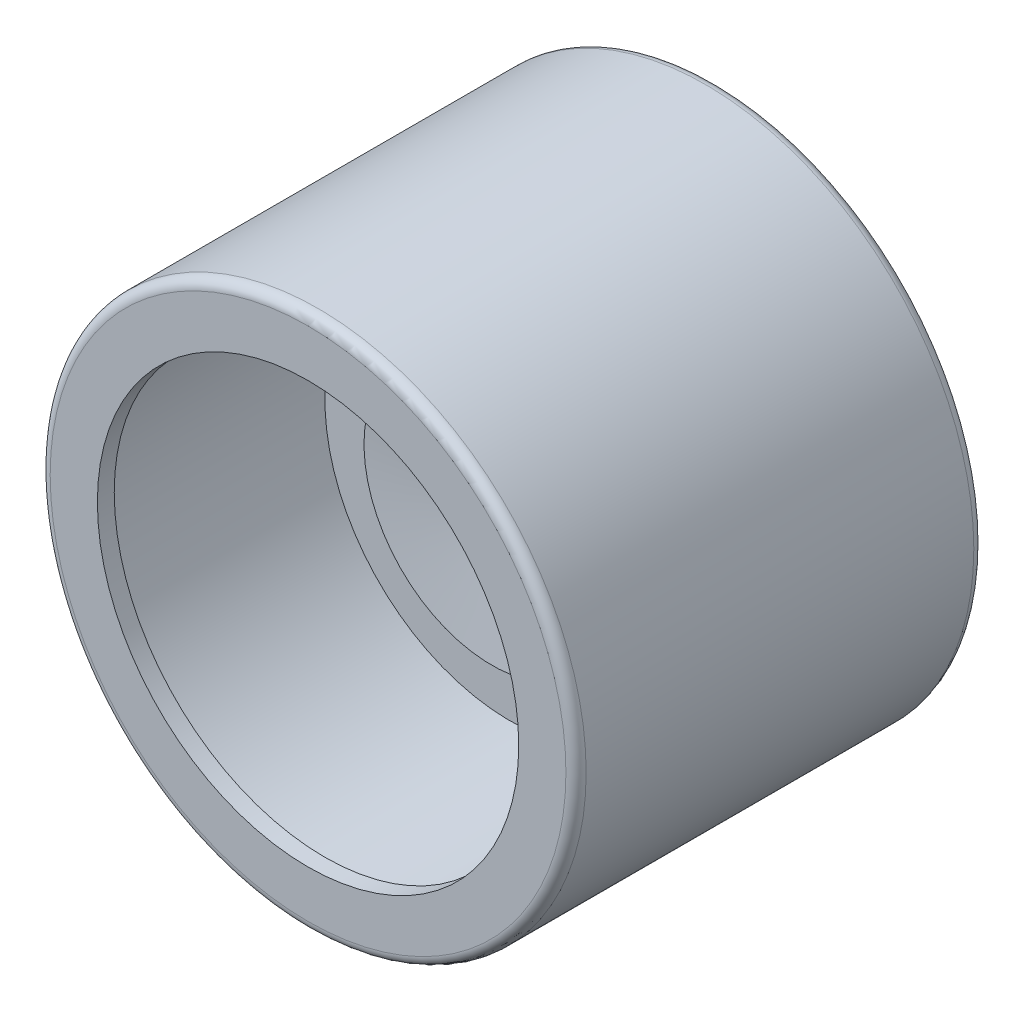
SolidWorks part; units mm, degrees
ref_plane "Front Plane" through (0, 0, 0) normal (0, 0, 1) x (1, 0, 0)
ref_plane "Top Plane" through (0, 0, 0) normal (0, 1, 0) x (1, 0, 0)
ref_plane "Right Plane" through (0, 0, 0) normal (1, 0, 0) x (0, 0, -1)
sketch "Sketch1" plane through (0, 0, 0) normal (0, 0, 1) x (1, 0, 0)
  circle A0 centre (0, 0) radius 7.95
  dimension "D1" = 15.9
extrude "Boss-Extrude1" add sketch "Sketch1" along normal blind 12.1
fillet "Fillet1" radius 0.3 2 edges at (7.95, 0, 0) (7.95, 0, 12.1)
sketch "Sketch2" plane through (0, 0, 12.1) normal (0, 0, 1) x (1, 0, 0)
  circle A0 centre (0, 0) radius 6.25
  circle A1 centre (0, 0) radius 7.65
  dimension "D1" = 15.3
  dimension "D2" = 1.4
sketch "Sketch3" plane through (0, 0, 12.1) normal (0, 0, 1) x (1, 0, 0)
  circle A0 centre (0, 0) radius 7.5
  dimension "D1" = 15
extrude "Cut-Extrude2" cut sketch "Sketch3" against normal blind 10
extrude "Boss-Extrude2" add sketch "Sketch2" against normal blind 0.5 contours A0 | A1
sketch "Sketch4" plane through (0, 0, 2.1) normal (0, 0, 1) x (1, 0, 0)
  circle A0 centre (0, 0) radius 5.5
  dimension "D1" = 11
extrude "Boss-Extrude3" add sketch "Sketch4" along normal blind 4
sketch "Sketch6" plane through (0, 0, 0) normal (1, 0, 0) x (0, 0, -1)
  line L0 (0, 0) -> (-5.5, 0) construction
  line L1 (-5.5, 3.7909) -> (-5.5, 0)
  line L2 (-5.5, 3.7909) -> (-6.65, 3.7909)
  line L3 (-6, 0.25) -> (-6.1195, 0.4512)
  line L4 (-6.3188, 1.0378) -> (-6.65, 3.7909)
  line L5 (-6, 0.25) -> (-6, 0)
  line L6 (-6, 0) -> (-5.5, 0) construction
  line L7 (-5.5, 0) -> (-6, 0)
  arc A0 (-6.3188, 1.0378) -> (-6.1195, 0.4512) centre (-4.8296, 1.2169) ccw
  dimension "D4" = 0.25
  dimension "D5" = 1.5
  dimension "D1" = 5.5
  dimension "D2" = 1.15
  dimension "D3" = 0.5
revolve "Revolve2" add sketch "Sketch6" angle 360 about L0
